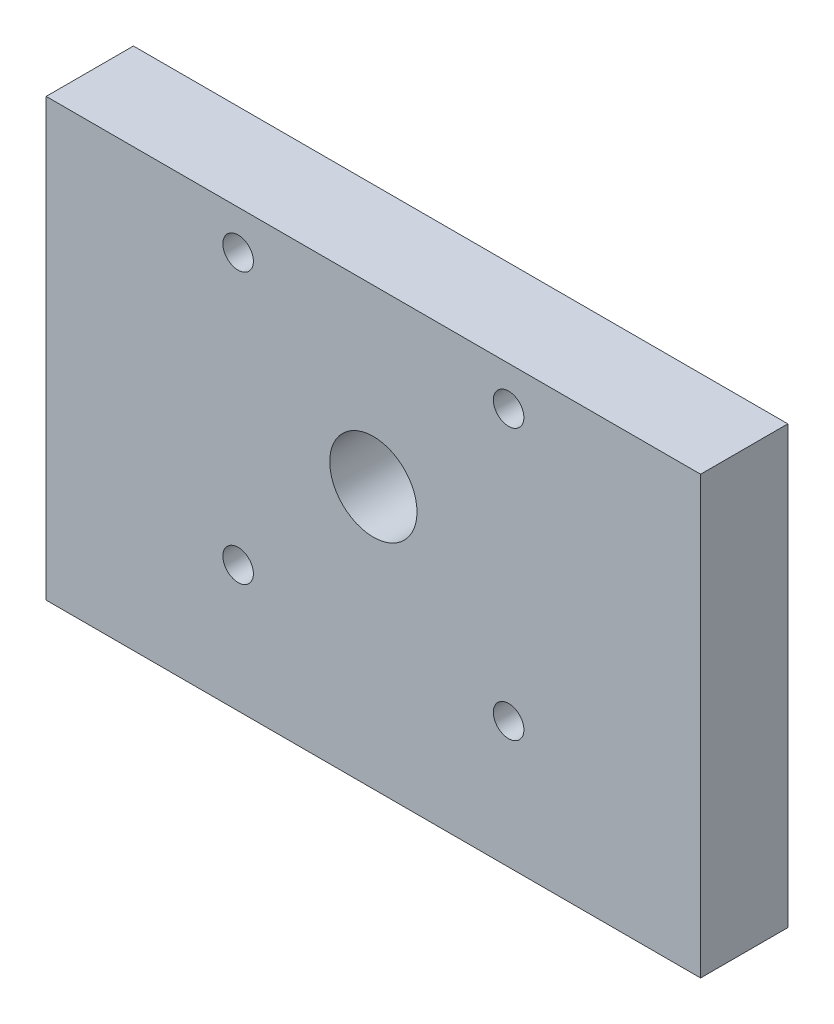
SolidWorks part; units mm, degrees
ref_plane "Front Plane" through (0, 0, 0) normal (0, 0, 1) x (1, 0, 0)
ref_plane "Top Plane" through (0, 0, 0) normal (0, 1, 0) x (1, 0, 0)
ref_plane "Right Plane" through (0, 0, 0) normal (1, 0, 0) x (0, 0, -1)
sketch "Sketch1" plane through (0, 0, 0) normal (0, 0, 1) x (1, 0, 0)
  line L1 (-37.5, -20) -> (37.5, -20)
  line L2 (-37.5, -20) -> (-37.5, 20)
  line L3 (-37.5, 20) -> (37.5, 20)
  line L4 (37.5, -20) -> (37.5, 20)
  line L5 (-37.5, -20) -> (37.5, 20) construction
  line L6 (-37.5, 20) -> (37.5, -20) construction
  circle A0 centre (0, 0) radius 5
  point P0 (0, 0)
  dimension "D3" = 10
  dimension "D1" = 75
  dimension "D2" = 40
extrude "Boss-Extrude1" add sketch "Sketch1" along normal blind 10
hole_wizard "Ø3.5 (3.5) Diameter Hole1" positions "Sketch2" profile "Sketch3" hole size "Ø3.5" standard "ANSI Metric" end condition through all
sketch "Sketch2" plane through (0, 0, 0) normal (0, 0, -1) x (-1, 0, 0)
  point P0 (15.5, 15.5)
  point P3 (-15.5, 15.5)
  point P6 (-15.5, -15.5)
  point P9 (15.5, -15.5)
sketch "Sketch3" plane through (-15.5, 15.5, 0) normal (1, 0, 0) x (0, 1, 0)
  line L0 (0, 0) -> (0, 10)
  line L1 (0, 10) -> (1.75, 10)
  line L2 (1.75, 10) -> (1.75, 0)
  line L5 (1.75, 0) -> (0, 0)
  line L11 (0, -6.35) -> (0, 107.95) construction
  dimension "Thru Hole Dia." = 3.5
  dimension "Thru Hole Depth" = 10
sketch "Sketch4" plane through (0, -20, 0) normal (0, -1, 0) x (1, 0, 0)
  line L1 (-37.5, 10) -> (37.5, 10)
  line L2 (-37.5, 10) -> (-37.5, 0)
  line L3 (-37.5, 0) -> (37.5, 0)
  line L4 (37.5, 10) -> (37.5, 0)
extrude "Boss-Extrude2" add sketch "Sketch4" along normal blind 10
